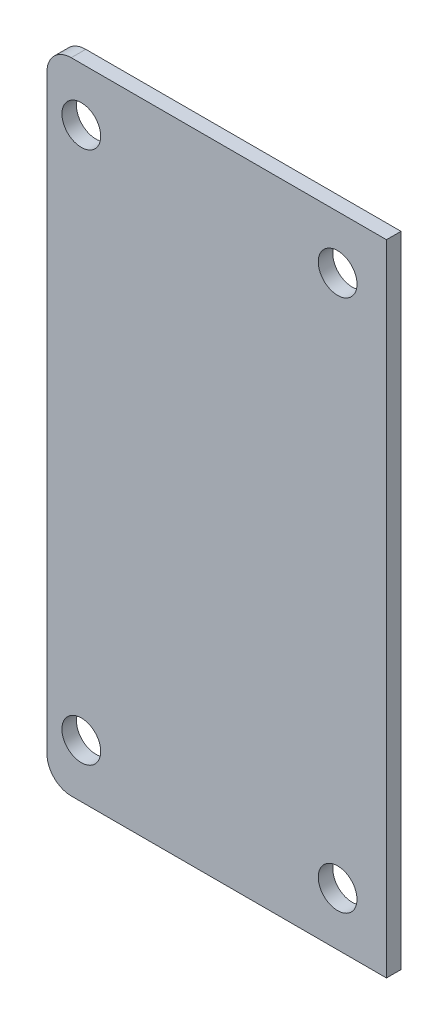
SolidWorks part; units mm, degrees
ref_plane "Front Plane" through (0, 0, 0) normal (0, 0, 1) x (1, 0, 0)
ref_plane "Top Plane" through (0, 0, 0) normal (0, 1, 0) x (1, 0, 0)
ref_plane "Right Plane" through (0, 0, 0) normal (1, 0, 0) x (0, 0, -1)
sketch "Sketch1" plane through (0, 0, 0) normal (0, 0, 1) x (1, 0, 0)
  line L0 (-35.042, 61) -> (-35.042, -61)
  line L1 (-30.042, -66) -> (35.042, -66)
  line L2 (35.042, -66) -> (35.042, 66)
  line L3 (35.042, 66) -> (-30.042, 66)
  circle A0 centre (24.958, 55) radius 4
  circle A1 centre (-27.958, 55) radius 4
  circle A2 centre (-27.958, -55) radius 4
  circle A3 centre (24.958, -55) radius 4
  arc A4 (-30.042, 66) -> (-35.042, 61) centre (-30.042, 61) ccw
  arc A5 (-35.042, -61) -> (-30.042, -66) centre (-30.042, -61) ccw
  dimension "D1" = 8
  dimension "D2" = 5
  dimension "D3" = 24.958
  dimension "D4" = 35.042
  dimension "D5" = 27.958
  dimension "D6" = 35.042
  dimension "D7" = 55
  dimension "D8" = 66
  dimension "D9" = 55
  dimension "D10" = 66
extrude "Boss-Extrude1" add sketch "Sketch1" along normal blind 3
